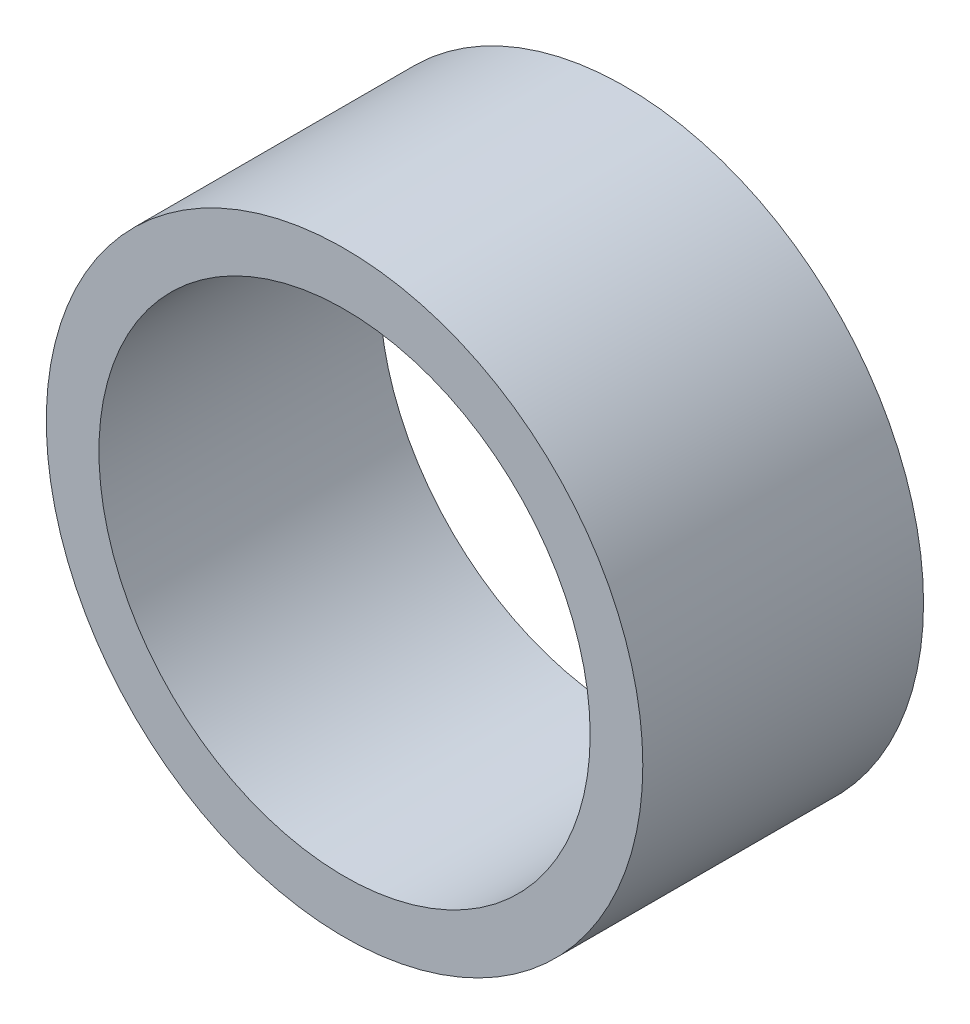
SolidWorks part; units mm, degrees
ref_plane "Спереди" through (0, 0, 0) normal (0, 0, 1) x (1, 0, 0)
ref_plane "Сверху" through (0, 0, 0) normal (0, 1, 0) x (1, 0, 0)
ref_plane "Справа" through (0, 0, 0) normal (1, 0, 0) x (0, 0, -1)
sketch "Эскиз1" plane through (0, 0, 0) normal (0, 0, 1) x (1, 0, 0)
  circle A0 centre (0, 0) radius 13
  circle A1 centre (0, 0) radius 7
  circle A2 centre (0, 0) radius 8.5
  circle A3 centre (0, 0) radius 11.5
  circle A4 centre (0, 10) radius 2.25
  dimension "D1" = 23
  dimension "D2" = 26
  dimension "D3" = 17
  dimension "D4" = 14
  dimension "D5" = 10
sketch "Эскиз2" plane through (0, 0, 0) normal (0, 0, 1) x (1, 0, 0)
  circle A0 centre (0, 0) radius 13
  circle A1 centre (0, 0) radius 7
  circle A2 centre (0, 0) radius 8.5
  circle A3 centre (0, 0) radius 11.5
  circle A4 centre (0, 10) radius 2.25
  dimension "D1" = 23
  dimension "D2" = 26
  dimension "D3" = 17
  dimension "D4" = 14
  dimension "D5" = 10
sketch "Эскиз3" plane through (0, 0, 0) normal (0, 0, 1) x (1, 0, 0)
  circle A0 centre (0, 0) radius 13
  circle A1 centre (0, 0) radius 7
  circle A2 centre (0, 0) radius 8.5
  circle A3 centre (0, 0) radius 11.5
  circle A4 centre (0, 10) radius 2.25
  dimension "D1" = 23
  dimension "D2" = 26
  dimension "D3" = 17
  dimension "D4" = 14
  dimension "D5" = 10
extrude "Бобышка-Вытянуть2" add sketch "Эскиз2" along normal blind 8 separate body contours A2 | A1
